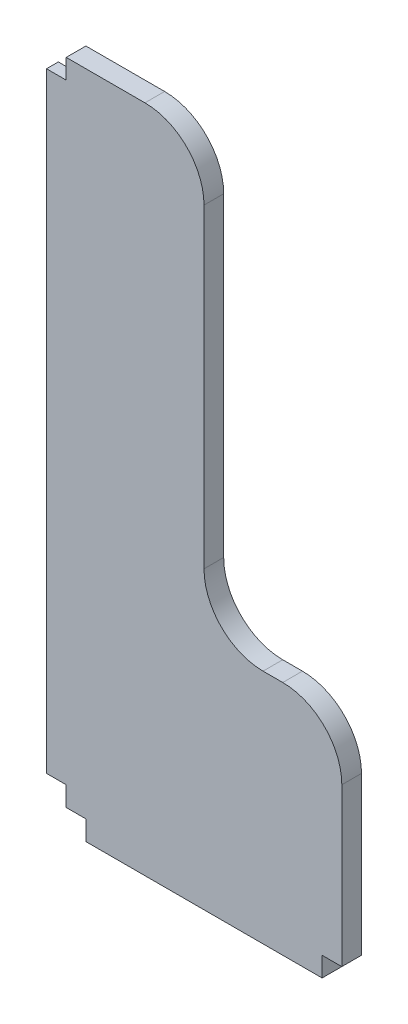
SolidWorks part; units mm, degrees
ref_plane "Alzado" through (0, 0, 0) normal (0, 0, 1) x (1, 0, 0)
ref_plane "Planta" through (0, 0, 0) normal (0, 1, 0) x (1, 0, 0)
ref_plane "Vista lateral" through (0, 0, 0) normal (1, 0, 0) x (0, 0, -1)
sketch "Croquis2" plane through (0, 0, 0) normal (0, 0, 1) x (1, 0, 0)
  line L6 (0, 0) -> (6.35, 0)
  line L7 (0, 0) -> (0, 6.35)
  line L8 (0, 6.35) -> (-6.35, 6.35)
  line L9 (6.35, 0) -> (6.35, -6.35)
  line L10 (6.35, -6.35) -> (82.55, -6.35)
  line L11 (-6.35, 6.35) -> (-6.35, 203.2)
  line L12 (82.55, -6.35) -> (82.55, 0)
  line L13 (82.55, 0) -> (88.9, 0)
  line L15 (-6.35, 203.2) -> (0, 203.2)
  line L16 (0, 203.2) -> (0, 209.55)
  line L17 (0, 209.55) -> (25.4, 209.55)
  line L18 (44.45, 190.5) -> (44.45, 88.9)
  line L19 (63.5, 69.85) -> (69.85, 69.85)
  line L20 (88.9, 50.8) -> (88.9, 0)
  arc A3 (25.4, 209.55) -> (44.45, 190.5) centre (25.4, 190.5) cw
  arc A4 (44.45, 88.9) -> (63.5, 69.85) centre (63.5, 88.9) ccw
  arc A5 (69.85, 69.85) -> (88.9, 50.8) centre (69.85, 50.8) cw
  point P21 (44.45, 209.55)
  point P24 (44.45, 69.85)
  dimension "D5" = 76.2
  dimension "D11" = 19.05
  dimension "D1" = 6.35
  dimension "D2" = 6.35
  dimension "D3" = 6.35
  dimension "D4" = 6.35
  dimension "D6" = 6.35
  dimension "D7" = 196.85
  dimension "D8" = 6.35
  dimension "D9" = 44.45
  dimension "D10" = 139.7
extrude "Saliente-Extruir3" add sketch "Croquis2" along normal blind 6.35
sketch "Croquis5" plane through (-6.35, 0, 0) normal (-1, 0, 0) x (0, 0, 1)
  line L0 (6.35, 6.35) -> (0, 6.35) construction
  line L1 (0, 203.2) -> (2.54, 203.2)
  line L2 (0, 203.2) -> (0, 6.35)
  line L3 (0, 6.35) -> (2.54, 6.35)
  line L4 (2.54, 203.2) -> (2.54, 6.35)
  dimension "D1" = 2.54
extrude "Cortar-Extruir1" cut sketch "Croquis5" against normal blind 6.35
